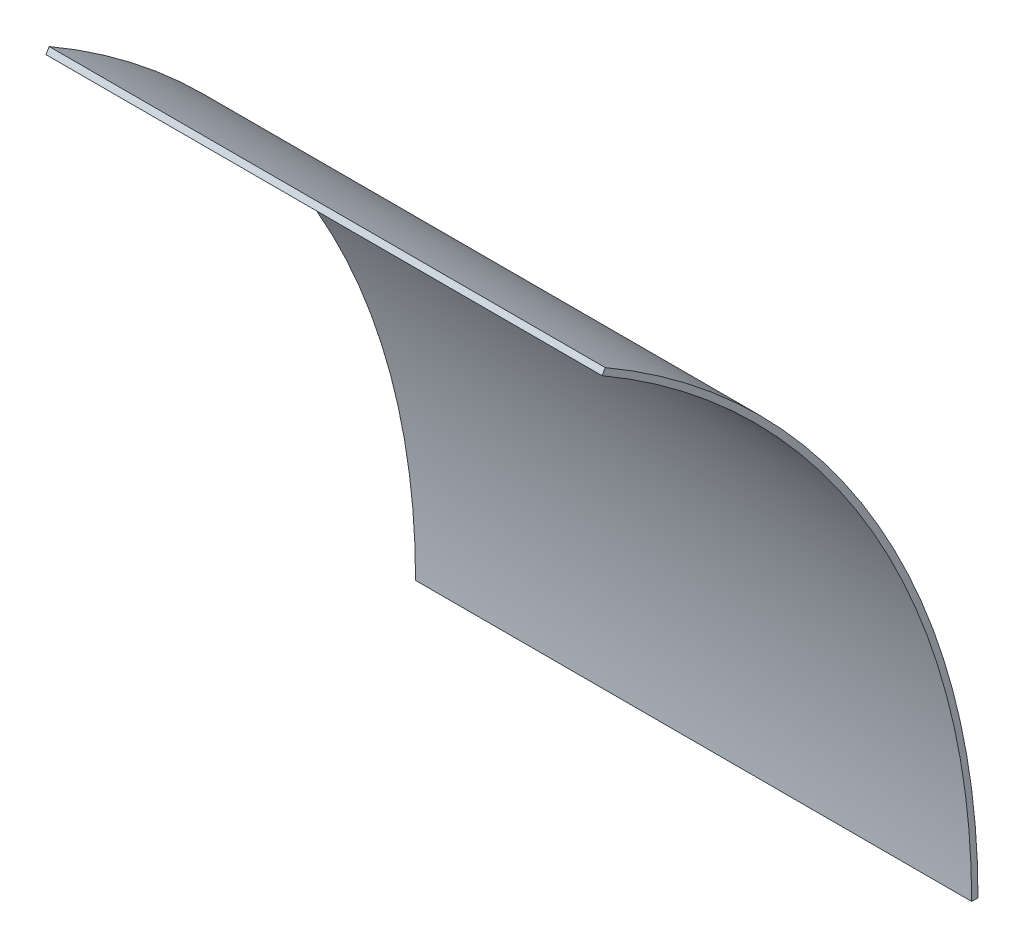
SolidWorks part; units mm, degrees
material "6061-T6 (SS)"
ref_plane "Front Plane" through (0, 0, 0) normal (0, 0, 1) x (1, 0, 0)
ref_plane "Top Plane" through (0, 0, 0) normal (0, 1, 0) x (1, 0, 0)
ref_plane "Right Plane" through (0, 0, 0) normal (1, 0, 0) x (0, 0, -1)
sketch "Sketch1" plane through (0, 0, 0) normal (1, 0, 0) x (0, 0, -1)
  line L0 (0, 0) -> (187.2615, 0) construction
  line L1 (0, 0) -> (93.6307, 162.1732) construction
  line L2 (93.6307, 162.1732) -> (92.837, 160.7984)
  line L3 (187.2615, 0) -> (185.674, 0)
  arc A0 (185.674, 0) -> (92.837, 160.7984) centre (0, 0) ccw
  arc A1 (187.2615, 0) -> (93.6307, 162.1732) centre (0, 0) ccw
  dimension "D1" = 371.348
  dimension "D2" = 1.5875
  dimension "D3" = 60
extrude "Boss-Extrude1" add sketch "Sketch1" along normal blind 139.7
